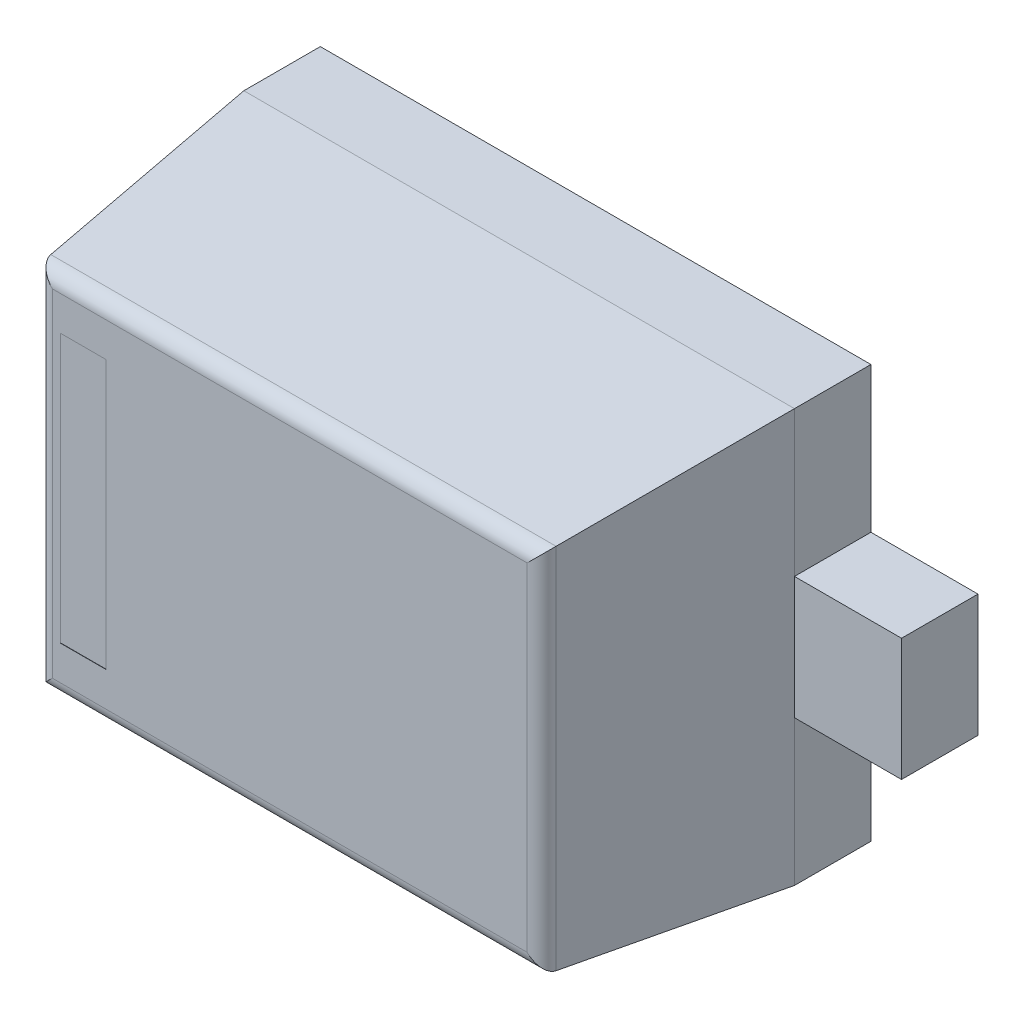
SolidWorks part; units mm, degrees
ref_plane "Top Plane" through (0, 0, 0) normal (0, 0, 1) x (1, 0, 0)
ref_plane "Front Plane" through (0, 0, 0) normal (0, 1, 0) x (1, 0, 0)
ref_plane "Right Plane" through (0, 0, 0) normal (1, 0, 0) x (0, 0, -1)
sketch "SkBody" plane through (0, 0, 0) normal (0, 0, 1) x (1, 0, 0)
  line L1 (-0.9, 0.675) -> (0.9, 0.675)
  line L2 (-0.9, 0.675) -> (-0.9, -0.675)
  line L3 (-0.9, -0.675) -> (0.9, -0.675)
  line L4 (0.9, 0.675) -> (0.9, -0.675)
  line L5 (-0.9, 0.675) -> (0.9, -0.675) construction
  line L6 (-0.9, -0.675) -> (0.9, 0.675) construction
  point P0 (0, 0)
  dimension "BodyL" = 1.8
  dimension "BodyW" = 1.35
extrude "Boss-Body" add sketch "SkBody" along normal blind 1
chamfer "Chamfer1" distance 0.75 angle 6 4 edges at (0, -0.675, 1) (-0.9, 0, 1) (0, 0.675, 1) (0.9, 0, 1)
fillet "Fillet1" radius 0.05 4 edges at (0, 0.5962, 1) (0.8212, 0, 1) (0, -0.5962, 1) (-0.8212, 0, 1)
sketch "SkPolarity" plane through (0, 0, 1) normal (0, 0, 1) x (1, 0, 0)
  line L0 (-0.9, 0.675) -> (-0.9, -0.675) construction
  line L1 (-0.75, 0.4387) -> (-0.6, 0.4388)
  line L2 (-0.75, 0.4387) -> (-0.75, -0.4387)
  line L3 (-0.75, -0.4387) -> (-0.6, -0.4387)
  line L4 (-0.6, 0.4388) -> (-0.6, -0.4387)
  line L5 (-0.75, 0.4387) -> (-0.6, -0.4387) construction
  line L6 (-0.75, -0.4387) -> (-0.6, 0.4388) construction
  line L7 (-0.6, 0) -> (0, 0) construction
  point P0 (-0.675, 0)
  dimension "D1" = 0.15
  dimension "D2" = 0.15
  dimension "D3" = 0.8775
extrude "Cut-PMark" cut sketch "SkPolarity" against normal blind 0.001
sketch "SkLeads" plane through (0, 0, 0) normal (0, 0, 1) x (1, 0, 0)
  line L0 (0, 0.1199) -> (0, -0.1186) construction
  line L1 (0.9, -0.2) -> (1.25, -0.2)
  line L2 (0.9, -0.2) -> (0.9, 0.2)
  line L3 (0.9, 0.2) -> (1.25, 0.2)
  line L4 (1.25, -0.2) -> (1.25, 0.2)
  line L5 (0.9, -0.2) -> (1.25, 0.2) construction
  line L6 (0.9, 0.2) -> (1.25, -0.2) construction
  line L7 (-0.9, 0.2) -> (-1.25, 0.2)
  line L8 (-0.9, 0.2) -> (-0.9, -0.2)
  line L9 (-0.9, -0.2) -> (-1.25, -0.2)
  line L10 (-1.25, 0.2) -> (-1.25, -0.2)
  line L11 (-0.9, 0.2) -> (-1.25, -0.2) construction
  line L12 (-0.9, -0.2) -> (-1.25, 0.2) construction
  line L13 (0.9, 0) -> (-0.9, 0) construction
  point P0 (1.075, 0)
  point P2 (-1.075, 0)
  point P15 (0, 0)
  dimension "LeadW" = 0.4
  dimension "LeadSpan" = 2.5
  dimension "D1" = 1.8
extrude "Boss-Leads" add sketch "SkLeads" along normal blind 0.25
equation "\"D1@SkLeads\"=\"BodyL@SkBody\""
equation "\"D3@SkPolarity\"=\"BodyW@SkBody\"*.65"
